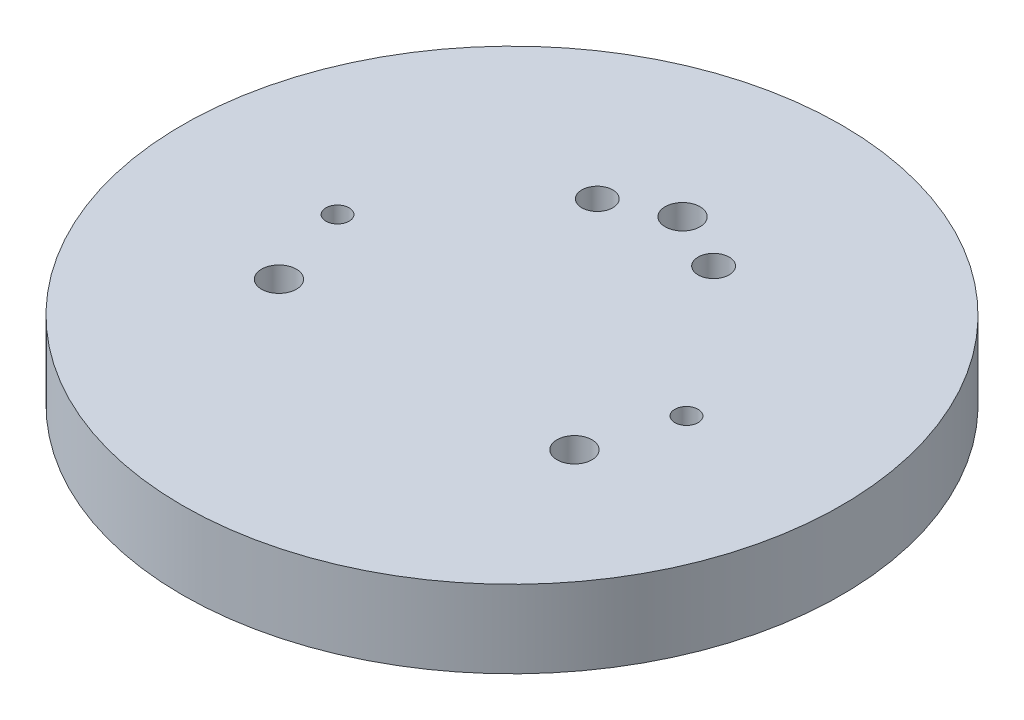
SolidWorks part; units mm, degrees
material "3003 Alloy"
ref_plane "Front Plane" through (0, 0, 0) normal (0, 0, 1) x (1, 0, 0)
ref_plane "Top Plane" through (0, 0, 0) normal (0, 1, 0) x (1, 0, 0)
ref_plane "Right Plane" through (0, 0, 0) normal (1, 0, 0) x (0, 0, -1)
sketch "Sketch1" plane through (0, 0, 0) normal (0, 1, 0) x (1, 0, 0)
  circle A0 centre (0, 0) radius 42.5
  dimension "D1" = 85
extrude "Boss-Extrude1" add sketch "Sketch1" along normal blind 10
sketch "Sketch2" plane through (0, 10, 0) normal (0, 1, 0) x (1, 0, 0)
  line L0 (-22.5, 0) -> (22.5, 0) construction
  circle A0 centre (-22.5, 0) radius 1.5
  circle A1 centre (22.5, 0) radius 1.5
  point P2 (0, 0)
  dimension "D2" = 3
  dimension "D1" = 45
extrude "Cut-Extrude1" cut sketch "Sketch2" against normal blind 5
sketch "Sketch3" plane through (0, 10, 0) normal (0, 1, 0) x (1, 0, 0)
  circle A0 centre (0, 22) radius 2.25
  circle A1 centre (0, 0) radius 22
  circle A2 centre (19.0526, -11) radius 2.25
  circle A3 centre (-19.0526, -11) radius 2.25
  point P11 (0, 0)
  dimension "D1" = 4.5
  dimension "D2" = 44
  dimension "D3" = 3
extrude "Cut-Extrude2" cut sketch "Sketch3" against normal through all contours A0 | A2 | A3
sketch "Sketch4" plane through (0, 0, 0) normal (0, -1, 0) x (1, 0, 0)
  circle A0 centre (0, -22) radius 5
  circle A1 centre (19.0526, 11) radius 5
  circle A2 centre (-19.0526, 11) radius 5
  dimension "D1" = 10
extrude "Cut-Extrude3" cut sketch "Sketch4" against normal blind 4.4
sketch "Sketch5" plane through (0, 10, 0) normal (0, 1, 0) x (1, 0, 0)
  circle A0 centre (-7.5, 18.5) radius 2
  circle A1 centre (7.5, 18.5) radius 2
  circle A2 centre (0, 22) radius 2.25 construction
  dimension "D2" = 7.5
  dimension "D4" = 4
  dimension "D1" = 15
  dimension "D3" = 18.5
extrude "Cut-Extrude4" cut sketch "Sketch5" against normal through all
